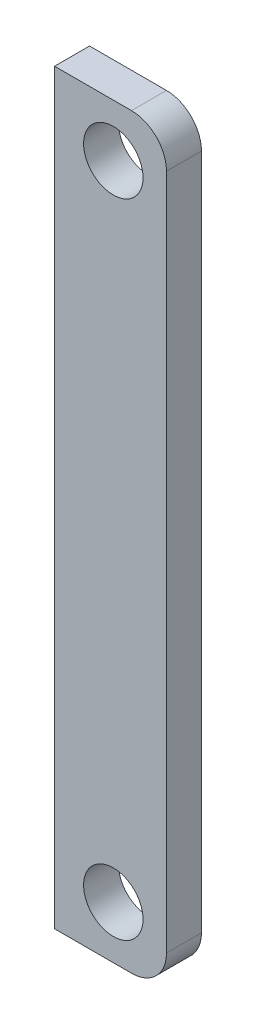
SolidWorks part; units mm, degrees
ref_plane "Front Plane" through (0, 0, 0) normal (0, 0, 1) x (1, 0, 0)
ref_plane "Top Plane" through (0, 0, 0) normal (0, 1, 0) x (1, 0, 0)
ref_plane "Right Plane" through (0, 0, 0) normal (1, 0, 0) x (0, 0, -1)
sketch "Sketch1" plane through (0, 0, 0) normal (0, 0, 1) x (1, 0, 0)
  line L0 (30.8, 21.36) -> (30.8, -21.36)
  line L1 (-35.2, 21.36) -> (35.2, 21.36)
  line L2 (-37.2, 19.36) -> (-37.2, -19.36)
  line L3 (-35.2, -21.36) -> (35.2, -21.36)
  line L4 (37.2, 19.36) -> (37.2, -19.36)
  line L5 (-37.2, 21.36) -> (37.2, -21.36) construction
  line L6 (-37.2, -21.36) -> (37.2, 21.36) construction
  line L7 (-34.16, 18.36) -> (34.16, 18.36) construction
  line L8 (-34.16, 18.36) -> (-34.16, -18.36) construction
  line L9 (-34.16, -18.36) -> (34.16, -18.36) construction
  line L10 (34.16, 18.36) -> (34.16, -18.36) construction
  line L11 (-34.16, 18.36) -> (34.16, -18.36) construction
  line L12 (-34.16, -18.36) -> (34.16, 18.36) construction
  circle A0 centre (-34.16, 18.36) radius 1.7
  circle A1 centre (-34.16, -18.36) radius 1.7
  circle A2 centre (34.16, -18.36) radius 1.7
  circle A3 centre (34.16, 18.36) radius 1.7
  arc A4 (-35.2, 21.36) -> (-37.2, 19.36) centre (-35.2, 19.36) ccw
  arc A5 (-37.2, -19.36) -> (-35.2, -21.36) centre (-35.2, -19.36) ccw
  arc A6 (35.2, -21.36) -> (37.2, -19.36) centre (35.2, -19.36) ccw
  arc A7 (35.2, 21.36) -> (37.2, 19.36) centre (35.2, 19.36) cw
  point P0 (0, 0)
  point P6 (0, 0)
  dimension "D5" = 3.4
  dimension "D7" = 2
  dimension "D1" = 74.4
  dimension "D2" = 42.72
  dimension "D3" = 36.72
  dimension "D4" = 68.32
  dimension "D6" = 6.4
extrude "Boss-Extrude1" add sketch "Sketch1" along normal mid plane 2 contours A7 L1 L0 L3 A6 L4 A3 A2
